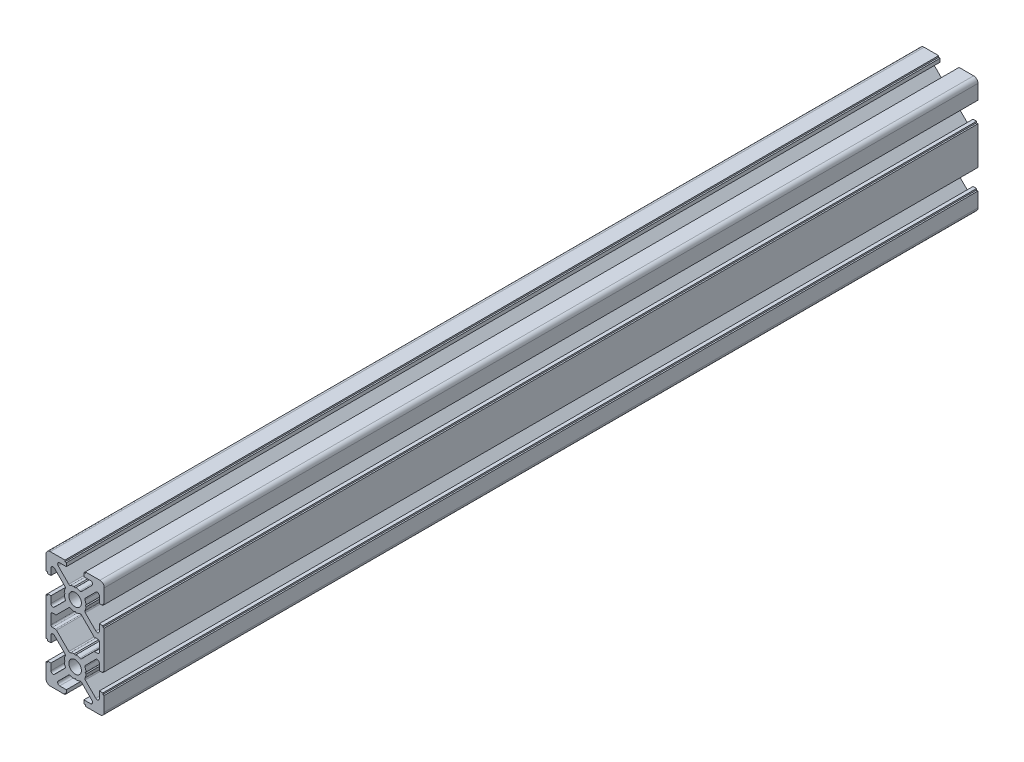
SolidWorks part; units mm, degrees
ref_plane "Front Plane" through (0, 0, 0) normal (0, 0, 1) x (1, 0, 0)
ref_plane "Top Plane" through (0, 0, 0) normal (0, 1, 0) x (1, 0, 0)
ref_plane "Right Plane" through (0, 0, 0) normal (1, 0, 0) x (0, 0, -1)
ref_plane "Plane1" through (0, 0, 100) normal (0, 0, 1) x (1, 0, 0)
sketch "Sketch1" plane through (0, 0, 100) normal (0, 0, 1) x (1, 0, 0)
  line L0 (3, 19.5) -> (3, 18.3)
  line L1 (3, 18.3) -> (5.2994, 18.3)
  line L2 (5.7944, 17.105) -> (2.1755, 13.4861)
  line L3 (0.3, 13.738) -> (0, 13.45)
  line L4 (0, 13.45) -> (-0.3, 13.738)
  line L5 (-2.1755, 13.4861) -> (-5.7944, 17.105)
  line L6 (-5.2994, 18.3) -> (-3, 18.3)
  line L7 (-3, 18.3) -> (-3, 19.5)
  line L8 (-3, 19.5) -> (-3.5, 19.5)
  line L9 (-3.5, 19.5) -> (-3.5, 20)
  line L10 (-3.5, 20) -> (-8.5, 20)
  line L11 (-10, 18.5) -> (-10, 13.5)
  line L12 (-10, 13.5) -> (-9.5, 13.5)
  line L13 (-9.5, 13.5) -> (-9.5, 13)
  line L14 (-9.5, 13) -> (-8.3, 13)
  line L15 (-8.3, 13) -> (-8.3, 15.2994)
  line L16 (-7.105, 15.7944) -> (-3.4861, 12.1755)
  line L17 (-3.738, 10.3) -> (-3.45, 10)
  line L18 (-3.45, 10) -> (-3.738, 9.7)
  line L19 (-3.4861, 7.8245) -> (-7.105, 4.2056)
  line L20 (-8.3, 4.7006) -> (-8.3, 7)
  line L21 (-8.3, 7) -> (-9.5, 7)
  line L22 (-9.5, 7) -> (-9.5, 6.5)
  line L23 (-9.5, 6.5) -> (-10, 6.5)
  line L24 (-10, 6.5) -> (-10, -6.5)
  line L25 (-10, -6.5) -> (-9.5, -6.5)
  line L26 (-9.5, -6.5) -> (-9.5, -7)
  line L27 (-9.5, -7) -> (-8.3, -7)
  line L28 (-8.3, -7) -> (-8.3, -4.7006)
  line L29 (-7.105, -4.2056) -> (-3.4861, -7.8245)
  line L30 (-3.738, -9.7) -> (-3.45, -10)
  line L31 (-3.45, -10) -> (-3.738, -10.3)
  line L32 (-3.4861, -12.1755) -> (-7.105, -15.7944)
  line L33 (-8.3, -15.2994) -> (-8.3, -13)
  line L34 (-8.3, -13) -> (-9.5, -13)
  line L35 (-9.5, -13) -> (-9.5, -13.5)
  line L36 (-9.5, -13.5) -> (-10, -13.5)
  line L37 (-10, -13.5) -> (-10, -18.5)
  line L38 (-8.5, -20) -> (-3.5, -20)
  line L39 (-3.5, -20) -> (-3.5, -19.5)
  line L40 (-3.5, -19.5) -> (-3, -19.5)
  line L41 (-3, -19.5) -> (-3, -18.3)
  line L42 (-3, -18.3) -> (-5.2994, -18.3)
  line L43 (-5.7944, -17.105) -> (-2.1755, -13.4861)
  line L44 (-0.3, -13.738) -> (0, -13.45)
  line L45 (0, -13.45) -> (0.3, -13.738)
  line L46 (2.1755, -13.4861) -> (5.7944, -17.105)
  line L47 (5.2994, -18.3) -> (3, -18.3)
  line L48 (3, -18.3) -> (3, -19.5)
  line L49 (3, -19.5) -> (3.5, -19.5)
  line L50 (3.5, -19.5) -> (3.5, -20)
  line L51 (3.5, -20) -> (8.5, -20)
  line L52 (10, -18.5) -> (10, -13.5)
  line L53 (10, -13.5) -> (9.5, -13.5)
  line L54 (9.5, -13.5) -> (9.5, -13)
  line L55 (9.5, -13) -> (8.3, -13)
  line L56 (8.3, -13) -> (8.3, -15.2994)
  line L57 (7.105, -15.7944) -> (3.4861, -12.1755)
  line L58 (3.738, -10.3) -> (3.45, -10)
  line L59 (3.45, -10) -> (3.738, -9.7)
  line L60 (3.4861, -7.8245) -> (7.105, -4.2056)
  line L61 (8.3, -4.7006) -> (8.3, -7)
  line L62 (8.3, -7) -> (9.5, -7)
  line L63 (9.5, -7) -> (9.5, -6.5)
  line L64 (9.5, -6.5) -> (10, -6.5)
  line L65 (10, -6.5) -> (10, 6.5)
  line L66 (10, 6.5) -> (9.5, 6.5)
  line L67 (9.5, 6.5) -> (9.5, 7)
  line L68 (9.5, 7) -> (8.3, 7)
  line L69 (8.3, 7) -> (8.3, 4.7006)
  line L70 (7.105, 4.2056) -> (3.4861, 7.8245)
  line L71 (3.738, 9.7) -> (3.45, 10)
  line L72 (3.45, 10) -> (3.738, 10.3)
  line L73 (3.4861, 12.1755) -> (7.105, 15.7944)
  line L74 (8.3, 15.2994) -> (8.3, 13)
  line L75 (8.3, 13) -> (9.5, 13)
  line L76 (9.5, 13) -> (9.5, 13.5)
  line L77 (9.5, 13.5) -> (10, 13.5)
  line L78 (10, 13.5) -> (10, 18.5)
  line L79 (8.5, 20) -> (3.5, 20)
  line L80 (3.5, 20) -> (3.5, 19.5)
  line L81 (3.5, 19.5) -> (3, 19.5)
  line L82 (2.1755, 6.5139) -> (6.3923, 2.2971)
  line L83 (6.7458, 2.1506) -> (7.8, 2.1506)
  line L84 (8.3, 1.6506) -> (8.3, -1.6506)
  line L85 (7.8, -2.1506) -> (6.7458, -2.1506)
  line L86 (6.3923, -2.2971) -> (2.1755, -6.5139)
  line L87 (0.3, -6.262) -> (0, -6.55)
  line L88 (0, -6.55) -> (-0.3, -6.262)
  line L89 (-2.1755, -6.5139) -> (-6.3923, -2.2971)
  line L90 (-6.7458, -2.1506) -> (-7.8, -2.1506)
  line L91 (-8.3, -1.6506) -> (-8.3, 1.6506)
  line L92 (-7.8, 2.1506) -> (-6.7458, 2.1506)
  line L93 (-6.3923, 2.2971) -> (-2.1755, 6.5139)
  line L94 (-0.3, 6.262) -> (0, 6.55)
  line L95 (0, 6.55) -> (0.3, 6.262)
  circle A0 centre (0, 10) radius 2.15
  circle A1 centre (0, -10) radius 2.15
  arc A2 (5.2994, 18.3) -> (5.7944, 17.105) centre (5.2994, 17.6) cw
  arc A3 (2.1755, 13.4861) -> (1.6076, 13.388) centre (1.8219, 13.8397) cw
  arc A4 (1.6076, 13.388) -> (0.3, 13.738) centre (0, 10) ccw
  arc A5 (-0.3, 13.738) -> (-1.6076, 13.388) centre (0, 10) ccw
  arc A6 (-1.6076, 13.388) -> (-2.1755, 13.4861) centre (-1.8219, 13.8397) cw
  arc A7 (-5.7944, 17.105) -> (-5.2994, 18.3) centre (-5.2994, 17.6) cw
  arc A8 (-8.5, 20) -> (-10, 18.5) centre (-8.5, 18.5) ccw
  arc A9 (-8.3, 15.2994) -> (-7.105, 15.7944) centre (-7.6, 15.2994) cw
  arc A10 (-3.4861, 12.1755) -> (-3.388, 11.6076) centre (-3.8397, 11.8219) cw
  arc A11 (-3.388, 11.6076) -> (-3.738, 10.3) centre (0, 10) ccw
  arc A12 (-3.738, 9.7) -> (-3.388, 8.3924) centre (0, 10) ccw
  arc A13 (-3.388, 8.3924) -> (-3.4861, 7.8245) centre (-3.8397, 8.1781) cw
  arc A14 (-7.105, 4.2056) -> (-8.3, 4.7006) centre (-7.6, 4.7006) cw
  arc A15 (-8.3, -4.7006) -> (-7.105, -4.2056) centre (-7.6, -4.7006) cw
  arc A16 (-3.4861, -7.8245) -> (-3.388, -8.3924) centre (-3.8397, -8.1781) cw
  arc A17 (-3.388, -8.3924) -> (-3.738, -9.7) centre (0, -10) ccw
  arc A18 (-3.738, -10.3) -> (-3.388, -11.6076) centre (0, -10) ccw
  arc A19 (-3.388, -11.6076) -> (-3.4861, -12.1755) centre (-3.8397, -11.8219) cw
  arc A20 (-7.105, -15.7944) -> (-8.3, -15.2994) centre (-7.6, -15.2994) cw
  arc A21 (-10, -18.5) -> (-8.5, -20) centre (-8.5, -18.5) ccw
  arc A22 (-5.2994, -18.3) -> (-5.7944, -17.105) centre (-5.2994, -17.6) cw
  arc A23 (-2.1755, -13.4861) -> (-1.6076, -13.388) centre (-1.8219, -13.8397) cw
  arc A24 (-1.6076, -13.388) -> (-0.3, -13.738) centre (0, -10) ccw
  arc A25 (0.3, -13.738) -> (1.6076, -13.388) centre (0, -10) ccw
  arc A26 (1.6076, -13.388) -> (2.1755, -13.4861) centre (1.8219, -13.8397) cw
  arc A27 (5.7944, -17.105) -> (5.2994, -18.3) centre (5.2994, -17.6) cw
  arc A28 (8.5, -20) -> (10, -18.5) centre (8.5, -18.5) ccw
  arc A29 (8.3, -15.2994) -> (7.105, -15.7944) centre (7.6, -15.2994) cw
  arc A30 (3.4861, -12.1755) -> (3.388, -11.6076) centre (3.8397, -11.8219) cw
  arc A31 (3.388, -11.6076) -> (3.738, -10.3) centre (0, -10) ccw
  arc A32 (3.738, -9.7) -> (3.388, -8.3924) centre (0, -10) ccw
  arc A33 (3.388, -8.3924) -> (3.4861, -7.8245) centre (3.8397, -8.1781) cw
  arc A34 (7.105, -4.2056) -> (8.3, -4.7006) centre (7.6, -4.7006) cw
  arc A35 (8.3, 4.7006) -> (7.105, 4.2056) centre (7.6, 4.7006) cw
  arc A36 (3.4861, 7.8245) -> (3.388, 8.3924) centre (3.8397, 8.1781) cw
  arc A37 (3.388, 8.3924) -> (3.738, 9.7) centre (0, 10) ccw
  arc A38 (3.738, 10.3) -> (3.388, 11.6076) centre (0, 10) ccw
  arc A39 (3.388, 11.6076) -> (3.4861, 12.1755) centre (3.8397, 11.8219) cw
  arc A40 (7.105, 15.7944) -> (8.3, 15.2994) centre (7.6, 15.2994) cw
  arc A41 (10, 18.5) -> (8.5, 20) centre (8.5, 18.5) ccw
  arc A42 (0.3, 6.262) -> (1.6076, 6.612) centre (0, 10) ccw
  arc A43 (1.6076, 6.612) -> (2.1755, 6.5139) centre (1.8219, 6.1603) cw
  arc A44 (6.3923, 2.2971) -> (6.7458, 2.1506) centre (6.7458, 2.6506) ccw
  arc A45 (7.8, 2.1506) -> (8.3, 1.6506) centre (7.8, 1.6506) cw
  arc A46 (8.3, -1.6506) -> (7.8, -2.1506) centre (7.8, -1.6506) cw
  arc A47 (6.7458, -2.1506) -> (6.3923, -2.2971) centre (6.7458, -2.6506) ccw
  arc A48 (2.1755, -6.5139) -> (1.6076, -6.612) centre (1.8219, -6.1603) cw
  arc A49 (1.6076, -6.612) -> (0.3, -6.262) centre (0, -10) ccw
  arc A50 (-0.3, -6.262) -> (-1.6076, -6.612) centre (0, -10) ccw
  arc A51 (-1.6076, -6.612) -> (-2.1755, -6.5139) centre (-1.8219, -6.1603) cw
  arc A52 (-6.3923, -2.2971) -> (-6.7458, -2.1506) centre (-6.7458, -2.6506) ccw
  arc A53 (-7.8, -2.1506) -> (-8.3, -1.6506) centre (-7.8, -1.6506) cw
  arc A54 (-8.3, 1.6506) -> (-7.8, 2.1506) centre (-7.8, 1.6506) cw
  arc A55 (-6.7458, 2.1506) -> (-6.3923, 2.2971) centre (-6.7458, 2.6506) ccw
  arc A56 (-2.1755, 6.5139) -> (-1.6076, 6.612) centre (-1.8219, 6.1603) cw
  arc A57 (-1.6076, 6.612) -> (-0.3, 6.262) centre (0, 10) ccw
extrude "Boss-Extrude1" add sketch "Sketch1" against normal blind 300
